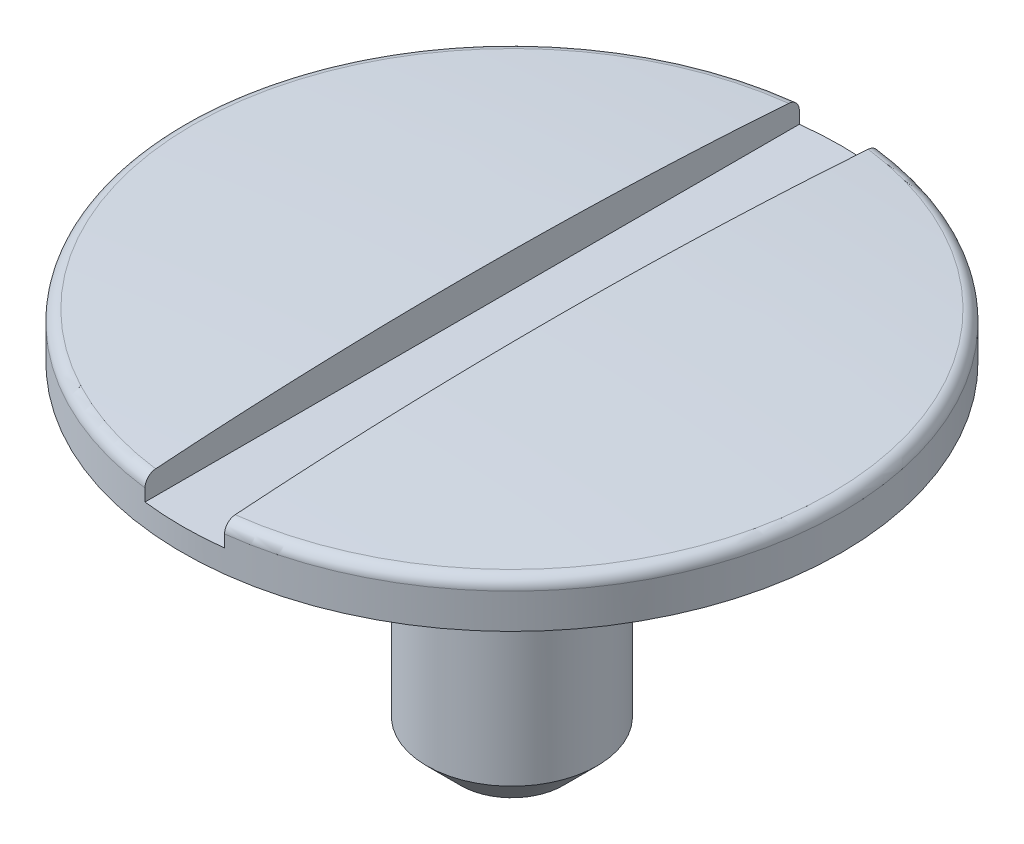
SolidWorks part; units mm, degrees
ref_plane "Alzado" through (0, 0, 0) normal (0, 0, 1) x (1, 0, 0)
ref_plane "Planta" through (0, 0, 0) normal (0, 1, 0) x (1, 0, 0)
ref_plane "Vista lateral" through (0, 0, 0) normal (1, 0, 0) x (0, 0, -1)
sketch "Sketch4" plane through (0, 0, 0) normal (0, 0, 1) x (1, 0, 0)
  line L0 (-848.3562, 0) -> (41569.4551, 0) construction
  line L1 (-848.2787, 0.2) -> (41569.5327, 0.2) construction
  line L2 (0, -848.3562) -> (0, 41569.4551) construction
  line L3 (1.45, -848.3562) -> (1.45, 41569.4551) construction
  line L4 (0, 0) -> (1.45, 0)
  line L5 (1.45, 0) -> (1.45, 0.2)
  line L6 (0, 0.2526) -> (0, 0)
  arc A1 (0, 0.2526) -> (1.45, 0.2) centre (0, -19.7474) cw
  point P8 (1.45, 0.2)
  dimension "D3" = 20
  dimension "D1" = 1.45
  dimension "D2" = 0.2
revolve "Revolve1" add sketch "Sketch4" angle 360 about L2
sketch "Sketch2" plane through (0, 0, 0) normal (0, 1, 0) x (1, 0, 0)
  circle A0 centre (0, 0) radius 0.375
  dimension "D1" = 0.75
extrude "Boss-Extrude2" add sketch "Sketch2" against normal blind 1.5
fillet "Fillet1" radius 0.05 1 edges at (1.45, 0.2, 0)
chamfer "Chamfer2" distance 0.15 angle 45 1 edges at (0, -1.5, 0.375)
sketch "Sketch3" plane through (0, 0, 0) normal (0, 0, 1) x (1, 0, 0)
  line L0 (0, -1000) -> (0, 49000) construction
  line L2 (-0.175, -999.9073) -> (-0.175, 49000.0927) construction
  line L3 (-1000, 0) -> (49000, 0) construction
  line L4 (-1000.8273, 0.1) -> (48999.1727, 0.1) construction
  line L5 (-0.175, 0.35) -> (0, 0.35)
  line L6 (-0.175, 0.35) -> (-0.175, 0.1)
  line L7 (0.175, 0.1) -> (0, 0.1)
  line L8 (-0.175, 0.1) -> (0, 0.1)
  line L9 (0.175, 0.35) -> (0.175, 0.1)
  line L10 (0.175, 0.35) -> (0, 0.35)
  dimension "D1" = 0.1
  dimension "D2" = 0.175
extrude "Cut-Extrude1" cut sketch "Sketch3" against normal through all both and the other way through all
